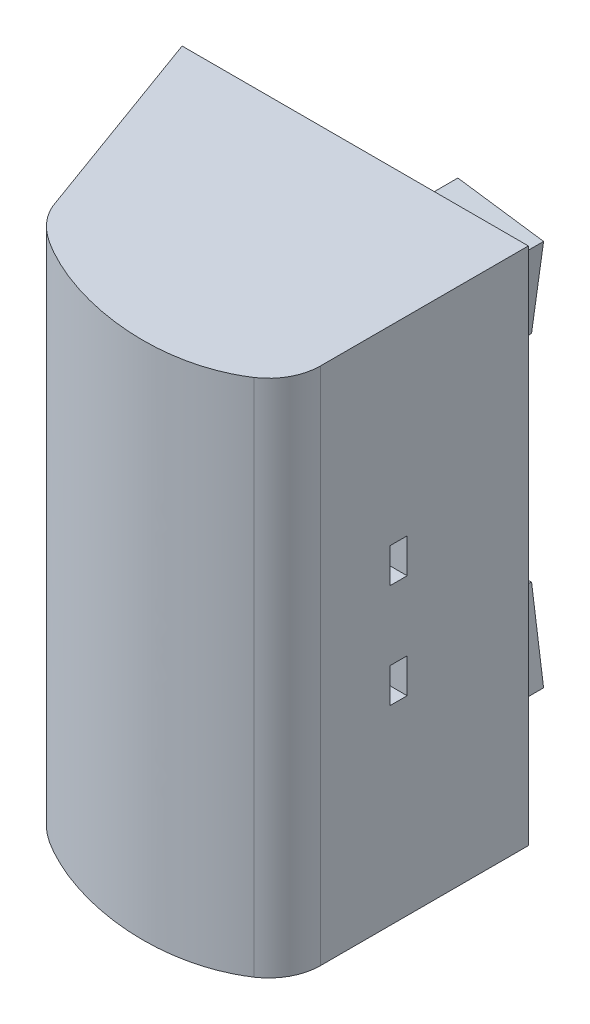
SolidWorks part; units mm, degrees
ref_plane "Front Plane" through (0, 0, 0) normal (0, 0, 1) x (1, 0, 0)
ref_plane "Top Plane" through (0, 0, 0) normal (0, 1, 0) x (1, 0, 0)
ref_plane "Right Plane" through (0, 0, 0) normal (1, 0, 0) x (0, 0, -1)
sketch "Sketch1" plane through (0, 0, 0) normal (0, 1, 0) x (1, 0, 0)
  line L0 (0, 0) -> (40, 0)
  line L1 (40, 0) -> (40, -24.01)
  line L2 (0, 0) -> (8.5505, -23.4923)
  arc A0 (40, -24.01) -> (37.2046, -29.077) centre (34.01, -24.01) cw
  spline S0 degree 3 poles (8.5505, -23.4923) (9.1877, -24.985) (10.869, -26.6959) (13.5799, -28.2755) (21.4202, -32.081) (31.2886, -32.957) (37.3305, -28.9954) knots 0 0 0 0 0.152199 0.226856 0.301953 1 1 1 1
  point P8 (40, -30)
  dimension "D5" = 5.99
  dimension "D6" = 25
  dimension "D1" = 30
  dimension "D3" = 40
  dimension "D4" = 70
extrude "Boss-Extrude1" add sketch "Sketch1" along normal blind 60 contours L2 S0 A0 L1 L0
sketch "Sketch2" plane through (0, 0, 0) normal (0, 0, -1) x (-1, 0, 0)
  line L0 (-40, 30) -> (0, 30) construction
  line L1 (-40, 60) -> (-40, 0) construction
  line L2 (0, 60) -> (0, 0) construction
  circle A0 centre (-34, 36) radius 1.6
  circle A1 centre (-34, 24) radius 1.6
  dimension "D1" = 3.2
  dimension "D2" = 6
  dimension "D3" = 6
extrude "Cut-Extrude1" cut sketch "Sketch2" against normal blind 20
sketch "Sketch4" plane through (40, 0, 0) normal (1, 0, 0) x (0, 0, -1)
  line L0 (0, 30) -> (-24.01, 30) construction
  line L1 (0, 60) -> (0, 0) construction
  line L2 (-24.01, 60) -> (-24.01, 0) construction
  line L3 (-14, 22) -> (-16, 22)
  line L4 (-14, 34) -> (-16, 34)
  line L5 (-14, 34) -> (-14, 38)
  line L6 (-14, 38) -> (-16, 38)
  line L7 (-16, 34) -> (-16, 38)
  line L8 (-16, 26) -> (-16, 22)
  line L9 (-14, 26) -> (-16, 26)
  line L10 (-14, 26) -> (-14, 22)
  point P10 (-14, 36)
  point P11 (-15, 34)
  dimension "D1" = 6
  dimension "D2" = 15
  dimension "D3" = 4
  dimension "D4" = 2
extrude "Cut-Extrude2" cut sketch "Sketch4" against normal blind 10
sketch "Sketch5" plane through (0, 0, 0) normal (0, 0, -1) x (-1, 0, 0)
  line L0 (-40, 30) -> (0, 30) construction
  line L1 (-40, 60) -> (-40, 0) construction
  line L2 (0, 60) -> (0, 0) construction
  line L3 (-34, 36) -> (-40, 78.6922) construction
  line L4 (-34, 36) -> (-34.835, 41.9416) construction
  line L5 (-34.835, 41.9416) -> (-31.3691, 42.4287) construction
  line L6 (-31.3691, 42.4287) -> (-32.7608, 52.3314)
  line L7 (-31.3691, 42.4287) -> (-21.4664, 43.8204)
  line L8 (-21.4664, 43.8204) -> (-22.8582, 53.7231)
  line L9 (-22.8582, 53.7231) -> (-32.7608, 52.3314)
  line L10 (-31.3691, 17.5713) -> (-32.7608, 7.6686)
  line L11 (-22.8582, 6.2769) -> (-32.7608, 7.6686)
  line L12 (-21.4664, 16.1796) -> (-22.8582, 6.2769)
  line L13 (-31.3691, 17.5713) -> (-21.4664, 16.1796)
  dimension "D1" = 8
  dimension "D2" = 6
  dimension "D3" = 90
  dimension "D4" = 3.5
  dimension "D5" = 90
  dimension "D6" = 10
  dimension "D7" = 10
extrude "Boss-Extrude2" add sketch "Sketch5" along normal blind 9
ref_plane "Plane1" through (34, 0, 0) normal (1, 0, 0) x (0, 0, -1)
sketch "Sketch6" plane through (34, 0, 0) normal (1, 0, 0) x (0, 0, -1)
  line L0 (0, 37.6) -> (2, 37.6)
  line L1 (0, 60) -> (0, 0) construction
  line L2 (0, 34.4) -> (0, 37.6) construction
  line L3 (2, 37.6) -> (0, 38.6)
  line L4 (0, 38.6) -> (0, 37.6)
  line L5 (0, 37.6) -> (0, 34.4) construction
  line L6 (0, 36) -> (2.7136, 36) construction
  dimension "D1" = 2
  dimension "D2" = 1
revolve "Revolve1" add sketch "Sketch6" angle 360 about L6
sketch "Sketch7" plane through (34, 0, 0) normal (1, 0, 0) x (0, 0, -1)
  line L0 (0, 25.6) -> (2, 25.6)
  line L1 (2, 25.6) -> (0, 26.6)
  line L2 (0, 26.6) -> (0, 25.6)
  line L3 (0, 22.4) -> (0, 25.6) construction
  line L4 (0, 24) -> (3.8393, 24) construction
  dimension "D1" = 2
  dimension "D2" = 1
revolve "Revolve2" add sketch "Sketch7" angle 360 about L4
